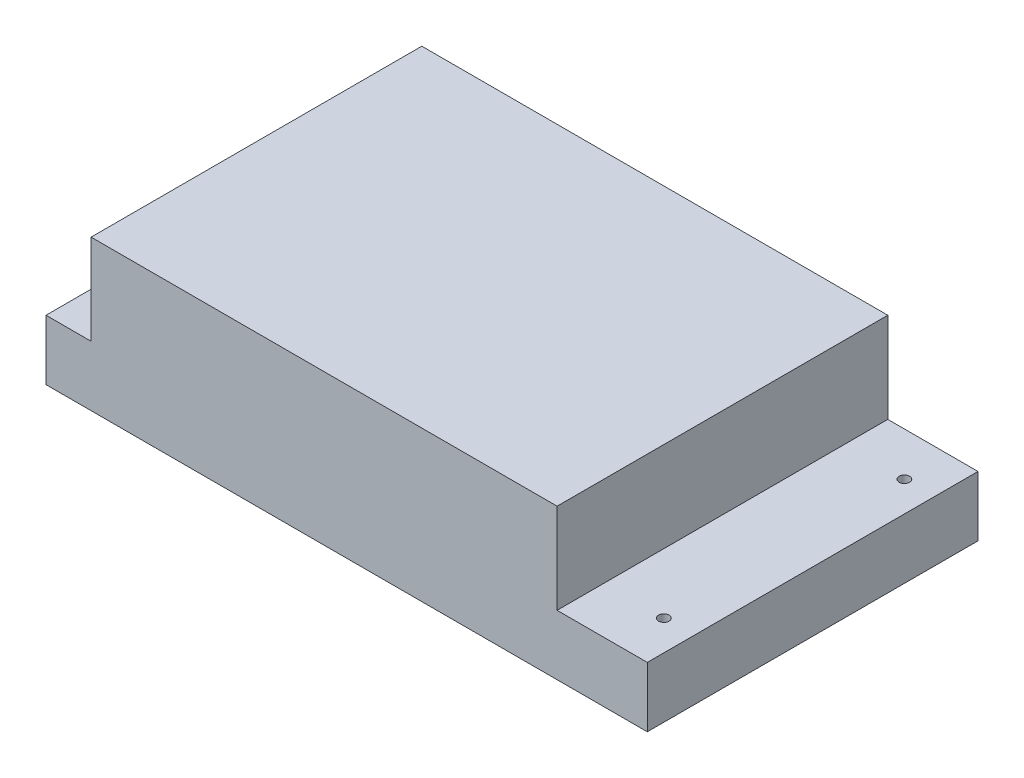
SolidWorks part; units mm, degrees
ref_plane "Front Plane" through (0, 0, 0) normal (0, 0, 1) x (1, 0, 0)
ref_plane "Top Plane" through (0, 0, 0) normal (0, 1, 0) x (1, 0, 0)
ref_plane "Right Plane" through (0, 0, 0) normal (1, 0, 0) x (0, 0, -1)
sketch "Sketch1" plane through (0, 0, 0) normal (0, 1, 0) x (1, 0, 0)
  line L1 (0, 0) -> (200, 0)
  line L2 (0, 0) -> (0, 110)
  line L3 (0, 110) -> (200, 110)
  line L4 (200, 0) -> (200, 110)
  dimension "D1" = 200
  dimension "D2" = 110
extrude "Boss-Extrude1" add sketch "Sketch1" along normal blind 50
sketch "Sketch2" plane through (0, 50, 0) normal (0, 1, 0) x (1, 0, 0)
  line L0 (0, 0) -> (200, 0) construction
  line L1 (200, 110) -> (170, 110)
  line L2 (200, 110) -> (200, 0)
  line L3 (200, 0) -> (170, 0)
  line L4 (170, 110) -> (170, 0)
  line L6 (0, 110) -> (15, 110)
  line L7 (0, 110) -> (0, 0)
  line L8 (0, 0) -> (15, 0)
  line L9 (15, 110) -> (15, 0)
  dimension "D1" = 30
  dimension "D2" = 15
extrude "Cut-Extrude1" cut sketch "Sketch2" against normal blind 30
sketch "Sketch3" plane through (0, 20, 0) normal (0, 1, 0) x (1, 0, 0)
  line L0 (200, 110) -> (170, 110) construction
  line L1 (200, 0) -> (200, 110) construction
  circle A0 centre (190, 95.5) radius 1.75
  circle A1 centre (190, 15.5) radius 1.75
  circle A2 centre (10, 95.5) radius 1.75
  circle A3 centre (10, 15.5) radius 1.75
  dimension "D1" = 3.5
  dimension "D2" = 3.5
  dimension "D6" = 3.5
  dimension "D7" = 3.5
  dimension "D3" = 14.5
  dimension "D4" = 10
  dimension "D5" = 80
  dimension "D8" = 180
extrude "Cut-Extrude2" cut sketch "Sketch3" against normal blind 30
